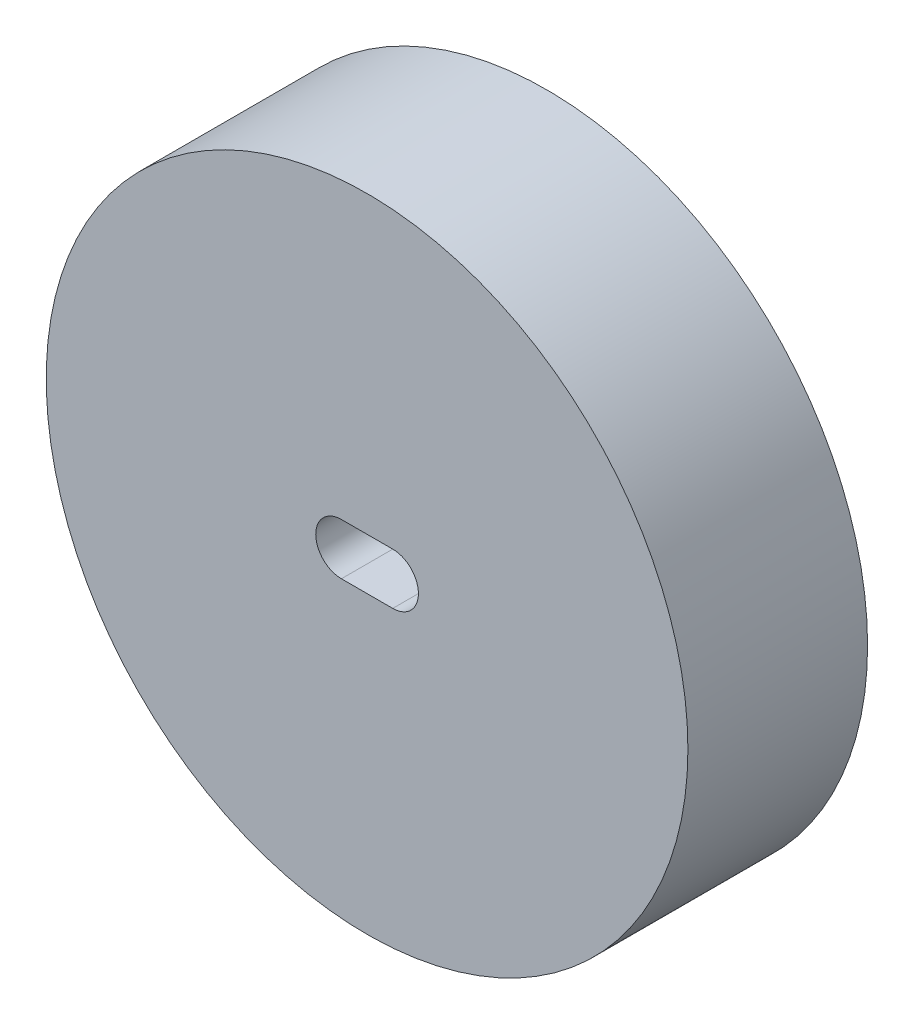
SolidWorks part; units mm, degrees
ref_plane "Front Plane" through (0, 0, 0) normal (0, 0, 1) x (1, 0, 0)
ref_plane "Top Plane" through (0, 0, 0) normal (0, 1, 0) x (1, 0, 0)
ref_plane "Right Plane" through (0, 0, 0) normal (1, 0, 0) x (0, 0, -1)
sketch "Sketch1" plane through (0, 0, 0) normal (0, 0, 1) x (1, 0, 0)
  line L0 (1, 0) -> (-1, 0) construction
  line L1 (1, -1) -> (-1, -1)
  line L2 (1, 1) -> (-1, 1)
  circle A0 centre (0, 0) radius 12.5
  arc A1 (1, -1) -> (1, 1) centre (1, 0) ccw
  arc A2 (-1, 1) -> (-1, -1) centre (-1, 0) ccw
  point P5 (0, 0)
  point P10 (0, 1)
  point P11 (0, -1)
  dimension "D1" = 25
  dimension "D2" = 2
  dimension "D3" = 2
  dimension "D4" = 0
extrude "Boss-Extrude1" add sketch "Sketch1" along normal mid plane 7
